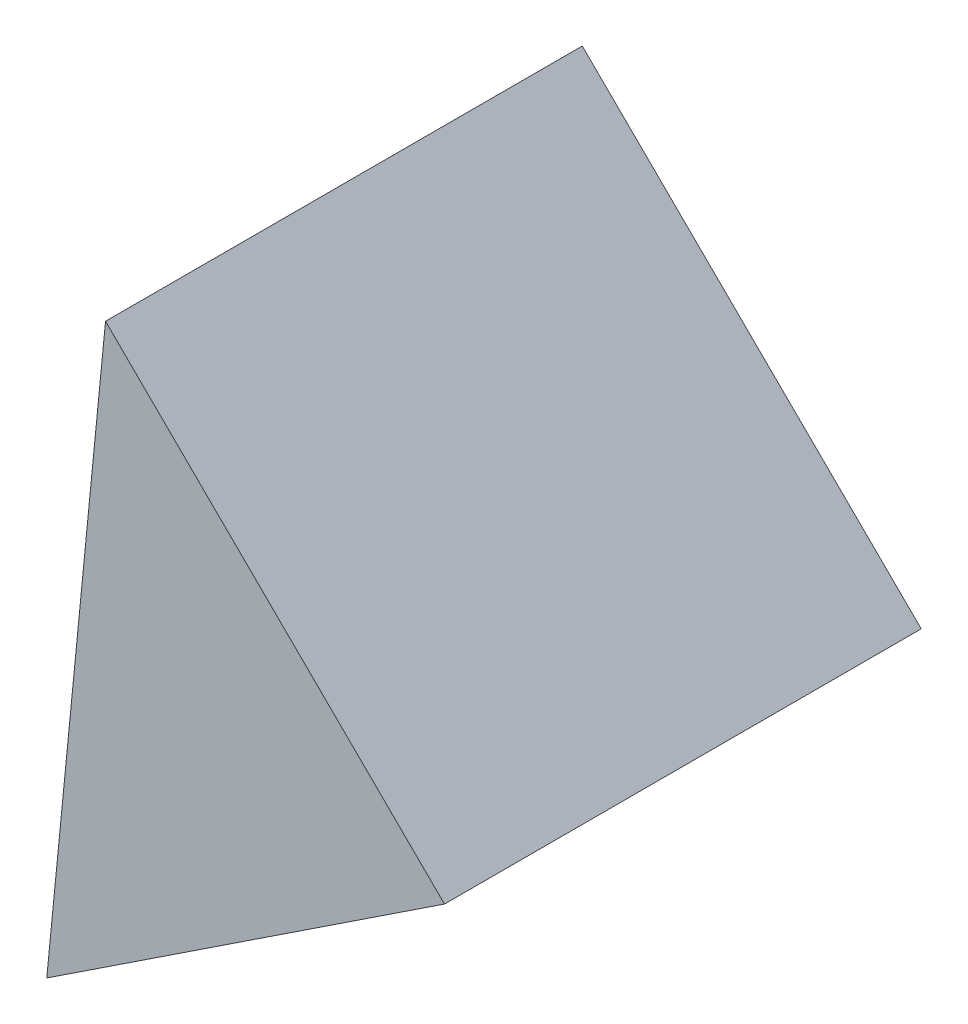
SolidWorks part; units mm, degrees
ref_plane "前视基准面" through (0, 0, 0) normal (0, 0, 1) x (1, 0, 0)
ref_plane "上视基准面" through (0, 0, 0) normal (0, 1, 0) x (1, 0, 0)
ref_plane "右视基准面" through (0, 0, 0) normal (1, 0, 0) x (0, 0, -1)
sketch "草图2" plane through (0, 0, 0) normal (0, 0, 1) x (1, 0, 0)
  line L0 (11.1142, 7.74) -> (2.227, 16.5302)
  line L1 (11.1142, 7.74) -> (0.6862, 0.8475)
  line L2 (0.6862, 0.8475) -> (2.227, 16.5302)
  dimension "D1" = 12.5
  dimension "D2" = 12.5
extrude "凸台-拉伸1" add sketch "草图2" along normal blind 12.5
